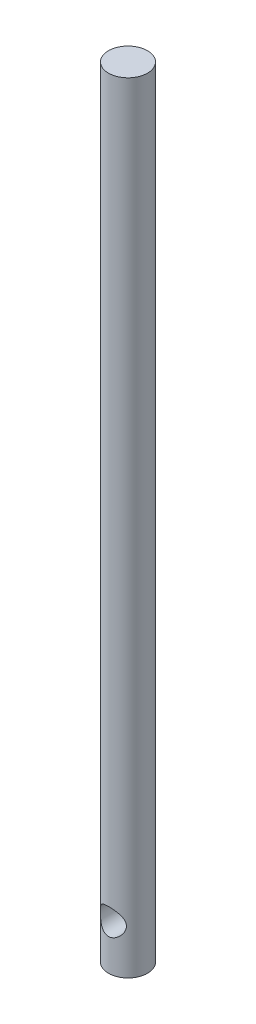
SolidWorks part; units mm, degrees
ref_plane "Front Plane" through (0, 0, 0) normal (0, 0, 1) x (1, 0, 0)
ref_plane "Top Plane" through (0, 0, 0) normal (0, 1, 0) x (1, 0, 0)
ref_plane "Right Plane" through (0, 0, 0) normal (1, 0, 0) x (0, 0, -1)
sketch "Sketch1" plane through (0, 0, 0) normal (0, 1, 0) x (1, 0, 0)
  circle A0 centre (0, 0) radius 1.5
  dimension "D1" = 3
extrude "Boss-Extrude1" add sketch "Sketch1" along normal blind 60
sketch "Sketch6" plane through (0, 0, 0) normal (0, 0, 1) x (1, 0, 0)
  circle A0 centre (0, 3.4587) radius 1
extrude "Cut-Extrude3" cut sketch "Sketch6" against normal through all both and the other way through all
